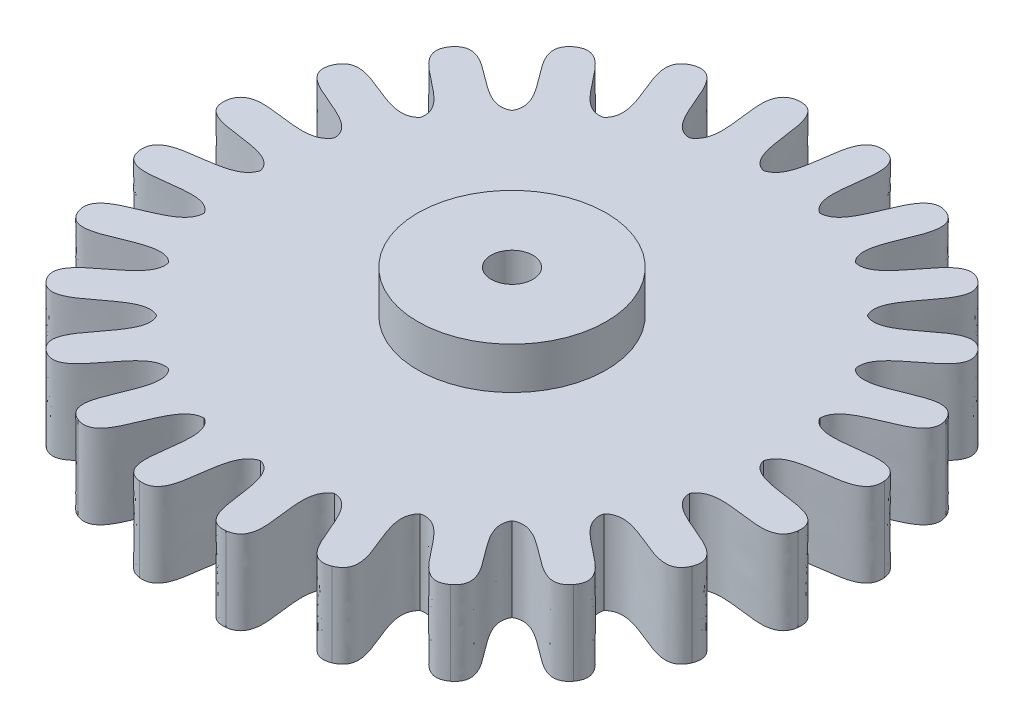
SolidWorks part; units mm, degrees
ref_plane "Front Plane" through (0, 0, 0) normal (0, 0, 1) x (1, 0, 0)
ref_plane "Top Plane" through (0, 0, 0) normal (0, 1, 0) x (1, 0, 0)
ref_plane "Right Plane" through (0, 0, 0) normal (1, 0, 0) x (0, 0, -1)
sketch "Sketch1" plane through (0, 0, 0) normal (0, 1, 0) x (1, 0, 0)
  circle A0 centre (0, 0) radius 2.25
  dimension "D1" = 4.5
extrude "Boss-Extrude1" add sketch "Sketch1" along normal blind 1
sketch "Sketch4" plane through (0, 1, 0) normal (0, 1, 0) x (1, 0, 0)
  circle A3 centre (-14, 0) radius 6
  point P4 (0, 0)
  circle B0 centre (-14, 0) radius 8
  spline B1 degree 3 poles (-14, 6) (-14.7204, 6.1976) (-14.1794, 7.9701) (-15.0353, 7.8637) knots 0 0 0 0 1 1 1 1
  spline B2 degree 3 poles (-15.5529, 5.7956) (-14.9082, 6.1729) (-15.8896, 7.745) (-15.0353, 7.8637) knots 0 0 0 0 1 1 1 1
  spline B3 degree 3 poles (-12.4471, 5.7956) (-13.0918, 6.1729) (-12.1104, 7.745) (-12.9647, 7.8637) knots 0 0 0 0 1 1 1 1
  spline B4 degree 3 poles (-14, 6) (-13.2796, 6.1976) (-13.8206, 7.9701) (-12.9647, 7.8637) knots 0 0 0 0 1 1 1 1
  spline B5 degree 3 poles (-11, 5.1962) (-11.5251, 5.7275) (-10.1703, 6.992) (-10.9647, 7.3278) knots 0 0 0 0 1 1 1 1
  spline B6 degree 3 poles (-12.4471, 5.7956) (-11.7, 5.7999) (-11.7639, 7.6521) (-10.9647, 7.3278) knots 0 0 0 0 1 1 1 1
  spline B7 degree 3 poles (-9.7574, 4.2426) (-10.1271, 4.8918) (-8.4911, 5.7626) (-9.1716, 6.2925) knots 0 0 0 0 1 1 1 1
  spline B8 degree 3 poles (-11, 5.1962) (-10.2773, 5.007) (-9.8596, 6.8127) (-9.1716, 6.2925) knots 0 0 0 0 1 1 1 1
  spline B9 degree 3 poles (-8.8038, 3) (-8.993, 3.7227) (-7.1873, 4.1404) (-7.7075, 4.8284) knots 0 0 0 0 1 1 1 1
  spline B10 degree 3 poles (-9.7574, 4.2426) (-9.1082, 3.8729) (-8.2374, 5.5089) (-7.7075, 4.8284) knots 0 0 0 0 1 1 1 1
  spline B11 degree 3 poles (-8.2044, 1.5529) (-8.2001, 2.3) (-6.3479, 2.2361) (-6.6722, 3.0353) knots 0 0 0 0 1 1 1 1
  spline B12 degree 3 poles (-8.8038, 3) (-8.2725, 2.4749) (-7.008, 3.8297) (-6.6722, 3.0353) knots 0 0 0 0 1 1 1 1
  spline B13 degree 3 poles (-8, 0) (-7.8024, 0.7204) (-6.0299, 0.1794) (-6.1363, 1.0353) knots 0 0 0 0 1 1 1 1
  spline B14 degree 3 poles (-8.2044, 1.5529) (-7.8271, 0.9082) (-6.255, 1.8896) (-6.1363, 1.0353) knots 0 0 0 0 1 1 1 1
  spline B15 degree 3 poles (-8.2044, -1.5529) (-7.8271, -0.9082) (-6.255, -1.8896) (-6.1363, -1.0353) knots 0 0 0 0 1 1 1 1
  spline B16 degree 3 poles (-8, 0) (-7.8024, -0.7204) (-6.0299, -0.1794) (-6.1363, -1.0353) knots 0 0 0 0 1 1 1 1
  spline B17 degree 3 poles (-8.8038, -3) (-8.2725, -2.4749) (-7.008, -3.8297) (-6.6722, -3.0353) knots 0 0 0 0 1 1 1 1
  spline B18 degree 3 poles (-8.2044, -1.5529) (-8.2001, -2.3) (-6.3479, -2.2361) (-6.6722, -3.0353) knots 0 0 0 0 1 1 1 1
  spline B19 degree 3 poles (-9.7574, -4.2426) (-9.1082, -3.8729) (-8.2374, -5.5089) (-7.7075, -4.8284) knots 0 0 0 0 1 1 1 1
  spline B20 degree 3 poles (-8.8038, -3) (-8.993, -3.7227) (-7.1873, -4.1404) (-7.7075, -4.8284) knots 0 0 0 0 1 1 1 1
  spline B21 degree 3 poles (-11, -5.1962) (-10.2773, -5.007) (-9.8596, -6.8127) (-9.1716, -6.2925) knots 0 0 0 0 1 1 1 1
  spline B22 degree 3 poles (-9.7574, -4.2426) (-10.1271, -4.8918) (-8.4911, -5.7626) (-9.1716, -6.2925) knots 0 0 0 0 1 1 1 1
  spline B23 degree 3 poles (-12.4471, -5.7956) (-11.7, -5.7999) (-11.7639, -7.6521) (-10.9647, -7.3278) knots 0 0 0 0 1 1 1 1
  spline B24 degree 3 poles (-11, -5.1962) (-11.5251, -5.7275) (-10.1703, -6.992) (-10.9647, -7.3278) knots 0 0 0 0 1 1 1 1
  spline B25 degree 3 poles (-14, -6) (-13.2796, -6.1976) (-13.8206, -7.9701) (-12.9647, -7.8637) knots 0 0 0 0 1 1 1 1
  spline B26 degree 3 poles (-12.4471, -5.7956) (-13.0918, -6.1729) (-12.1104, -7.745) (-12.9647, -7.8637) knots 0 0 0 0 1 1 1 1
  spline B27 degree 3 poles (-15.5529, -5.7956) (-14.9082, -6.1729) (-15.8896, -7.745) (-15.0353, -7.8637) knots 0 0 0 0 1 1 1 1
  spline B28 degree 3 poles (-14, -6) (-14.7204, -6.1976) (-14.1794, -7.9701) (-15.0353, -7.8637) knots 0 0 0 0 1 1 1 1
  spline B29 degree 3 poles (-17, -5.1962) (-16.4749, -5.7275) (-17.8297, -6.992) (-17.0353, -7.3278) knots 0 0 0 0 1 1 1 1
  spline B30 degree 3 poles (-15.5529, -5.7956) (-16.3, -5.7999) (-16.2361, -7.6521) (-17.0353, -7.3278) knots 0 0 0 0 1 1 1 1
  spline B31 degree 3 poles (-18.2426, -4.2426) (-17.8729, -4.8918) (-19.5089, -5.7626) (-18.8284, -6.2925) knots 0 0 0 0 1 1 1 1
  spline B32 degree 3 poles (-17, -5.1962) (-17.7227, -5.007) (-18.1404, -6.8127) (-18.8284, -6.2925) knots 0 0 0 0 1 1 1 1
  spline B33 degree 3 poles (-19.1962, -3) (-19.007, -3.7227) (-20.8127, -4.1404) (-20.2925, -4.8284) knots 0 0 0 0 1 1 1 1
  spline B34 degree 3 poles (-18.2426, -4.2426) (-18.8918, -3.8729) (-19.7626, -5.5089) (-20.2925, -4.8284) knots 0 0 0 0 1 1 1 1
  spline B35 degree 3 poles (-19.7956, -1.5529) (-19.7999, -2.3) (-21.6521, -2.2361) (-21.3278, -3.0353) knots 0 0 0 0 1 1 1 1
  spline B36 degree 3 poles (-19.1962, -3) (-19.7275, -2.4749) (-20.992, -3.8297) (-21.3278, -3.0353) knots 0 0 0 0 1 1 1 1
  spline B37 degree 3 poles (-20, 0) (-20.1976, -0.7204) (-21.9701, -0.1794) (-21.8637, -1.0353) knots 0 0 0 0 1 1 1 1
  spline B38 degree 3 poles (-19.7956, -1.5529) (-20.1729, -0.9082) (-21.745, -1.8896) (-21.8637, -1.0353) knots 0 0 0 0 1 1 1 1
  spline B39 degree 3 poles (-19.7956, 1.5529) (-20.1729, 0.9082) (-21.745, 1.8896) (-21.8637, 1.0353) knots 0 0 0 0 1 1 1 1
  spline B40 degree 3 poles (-20, 0) (-20.1976, 0.7204) (-21.9701, 0.1794) (-21.8637, 1.0353) knots 0 0 0 0 1 1 1 1
  spline B41 degree 3 poles (-19.1962, 3) (-19.7275, 2.4749) (-20.992, 3.8297) (-21.3278, 3.0353) knots 0 0 0 0 1 1 1 1
  spline B42 degree 3 poles (-19.7956, 1.5529) (-19.7999, 2.3) (-21.6521, 2.2361) (-21.3278, 3.0353) knots 0 0 0 0 1 1 1 1
  spline B43 degree 3 poles (-18.2426, 4.2426) (-18.8918, 3.8729) (-19.7626, 5.5089) (-20.2925, 4.8284) knots 0 0 0 0 1 1 1 1
  spline B44 degree 3 poles (-19.1962, 3) (-19.007, 3.7227) (-20.8127, 4.1404) (-20.2925, 4.8284) knots 0 0 0 0 1 1 1 1
  spline B45 degree 3 poles (-17, 5.1962) (-17.7227, 5.007) (-18.1404, 6.8127) (-18.8284, 6.2925) knots 0 0 0 0 1 1 1 1
  spline B46 degree 3 poles (-18.2426, 4.2426) (-17.8729, 4.8918) (-19.5089, 5.7626) (-18.8284, 6.2925) knots 0 0 0 0 1 1 1 1
  spline B47 degree 3 poles (-15.5529, 5.7956) (-16.3, 5.7999) (-16.2361, 7.6521) (-17.0353, 7.3278) knots 0 0 0 0 1 1 1 1
  spline B48 degree 3 poles (-17, 5.1962) (-16.4749, 5.7275) (-17.8297, 6.992) (-17.0353, 7.3278) knots 0 0 0 0 1 1 1 1
  circle B49 centre (-13.3148, 4.3262) radius 8
  spline B50 degree 3 poles (-7.323, 4.0122) (-7.088, 4.7213) (-5.3462, 4.0882) (-5.4077, 4.9485) knots 0 0 0 0 1 1 1 1
  spline B51 degree 3 poles (-7.4459, 5.5737) (-7.1029, 4.9101) (-5.4815, 5.8079) (-5.4077, 4.9485) knots 0 0 0 0 1 1 1 1
  spline B52 degree 3 poles (-7.323, 4.0122) (-7.1634, 3.2824) (-5.365, 3.73) (-5.516, 2.8808) knots 0 0 0 0 1 1 1 1
  spline B53 degree 3 poles (-8.2828, 1.0584) (-7.7247, 1.555) (-6.5328, 0.1358) (-6.1559, 0.9116) knots 0 0 0 0 1 1 1 1
  spline B54 degree 3 poles (-8.2828, 1.0584) (-8.5094, 0.3466) (-6.7282, -0.165) (-7.2836, -0.8249) knots 0 0 0 0 1 1 1 1
  spline B55 degree 3 poles (-10.5908, -1.0198) (-9.8592, -0.8688) (-9.5366, -2.6938) (-8.8223, -2.2104) knots 0 0 0 0 1 1 1 1
  spline B56 degree 3 poles (-13.6288, -1.6655) (-12.9197, -1.9006) (-13.5528, -3.6424) (-12.6925, -3.5809) knots 0 0 0 0 1 1 1 1
  spline B57 degree 3 poles (-13.6288, -1.6655) (-14.3586, -1.8251) (-13.911, -3.6236) (-14.7602, -3.4725) knots 0 0 0 0 1 1 1 1
  spline B58 degree 3 poles (-15.1689, -1.3801) (-15.9151, -1.3454) (-15.9483, -3.1984) (-16.7294, -2.8327) knots 0 0 0 0 1 1 1 1
  spline B59 degree 3 poles (-17.3296, 8.7851) (-17.9972, 8.4499) (-18.7811, 10.1292) (-19.346, 9.4774) knots 0 0 0 0 1 1 1 1
  spline B60 degree 3 poles (-13.0008, 10.318) (-13.7099, 10.553) (-13.0768, 12.2948) (-13.9371, 12.2333) knots 0 0 0 0 1 1 1 1
  circle B61 centre (-11.3262, 8.229) radius 8
  spline B62 degree 3 poles (-5.3591, 7.6018) (-5.0873, 8.2977) (-3.381, 7.5743) (-3.3974, 8.4366) knots 0 0 0 0 1 1 1 1
  spline B63 degree 3 poles (-5.4001, 9.1676) (-5.0923, 8.4869) (-3.4262, 9.2986) (-3.3974, 8.4366) knots 0 0 0 0 1 1 1 1
  spline B64 degree 3 poles (-5.7248, 6.0788) (-5.2821, 6.6806) (-3.8212, 5.5402) (-3.6138, 6.3774) knots 0 0 0 0 1 1 1 1
  spline B65 degree 3 poles (-5.3591, 7.6018) (-5.2379, 6.8647) (-3.4185, 7.2175) (-3.6138, 6.3774) knots 0 0 0 0 1 1 1 1
  spline B66 degree 3 poles (-5.7248, 6.0788) (-5.7985, 5.3354) (-3.9498, 5.2053) (-4.3558, 4.4444) knots 0 0 0 0 1 1 1 1
  spline B67 degree 3 poles (-17.2934, 8.8562) (-17.5652, 8.1603) (-19.2715, 8.8837) (-19.2551, 8.0214) knots 0 0 0 0 1 1 1 1
  spline B68 degree 3 poles (-16.1803, 11.7557) (-15.9167, 12.4547) (-17.6688, 13.0588) (-17.0796, 13.6887) knots 0 0 0 0 1 1 1 1
  circle B69 centre (-8.229, 11.3262) radius 8
  spline B70 degree 3 poles (-3.5661, 7.5503) (-2.9592, 7.9859) (-1.9222, 6.4499) (-1.4662, 7.182) knots 0 0 0 0 1 1 1 1
  spline B71 degree 3 poles (-2.7477, 8.8858) (-2.8603, 8.1473) (-1.0209, 7.9206) (-1.4662, 7.182) knots 0 0 0 0 1 1 1 1
  spline B72 degree 3 poles (-4.7023, 6.4721) (-4.0033, 6.7358) (-3.3992, 4.9837) (-2.7693, 5.5729) knots 0 0 0 0 1 1 1 1
  spline B73 degree 3 poles (-3.5661, 7.5503) (-3.866, 6.8661) (-2.1479, 6.1711) (-2.7693, 5.5729) knots 0 0 0 0 1 1 1 1
  spline B74 degree 3 poles (-4.7023, 6.4721) (-5.169, 5.8888) (-3.6894, 4.7728) (-4.4444, 4.3558) knots 0 0 0 0 1 1 1 1
  spline B75 degree 3 poles (-7.6018, 5.3591) (-6.8647, 5.2379) (-7.2175, 3.4185) (-6.3774, 3.6138) knots 0 0 0 0 1 1 1 1
  spline B76 degree 3 poles (-6.0788, 5.7248) (-6.6806, 5.2821) (-5.5402, 3.8212) (-6.3774, 3.6138) knots 0 0 0 0 1 1 1 1
  spline B77 degree 3 poles (-10.6694, 5.845) (-10.0916, 5.3714) (-11.3069, 3.9722) (-10.4817, 3.7213) knots 0 0 0 0 1 1 1 1
  spline B78 degree 3 poles (-12.0049, 6.6634) (-11.5694, 6.0564) (-13.1054, 5.0194) (-12.3732, 4.5635) knots 0 0 0 0 1 1 1 1
  spline B79 degree 3 poles (-12.0049, 6.6634) (-12.6892, 6.9632) (-13.3842, 5.2452) (-13.9823, 5.8665) knots 0 0 0 0 1 1 1 1
  spline B80 degree 3 poles (-13.0831, 7.7995) (-13.6664, 8.2662) (-14.7824, 6.7866) (-15.1994, 7.5416) knots 0 0 0 0 1 1 1 1
  spline B81 degree 3 poles (-13.7103, 13.7667) (-13.5977, 14.5052) (-15.4371, 14.7318) (-14.9918, 15.4705) knots 0 0 0 0 1 1 1 1
  circle B82 centre (-4.3262, 13.3148) radius 8
  spline B83 degree 3 poles (0.1326, 9.3) (-0.2026, 8.6324) (1.4767, 7.8484) (0.8249, 7.2836) knots 0 0 0 0 1 1 1 1
  spline B84 degree 3 poles (-2.4721, 7.6085) (-1.7259, 7.6432) (-1.6927, 5.7902) (-0.9116, 6.1559) knots 0 0 0 0 1 1 1 1
  spline B85 degree 3 poles (-1.0584, 8.2828) (-1.555, 7.7247) (-0.1358, 6.5328) (-0.9116, 6.1559) knots 0 0 0 0 1 1 1 1
  spline B86 degree 3 poles (-2.4721, 7.6085) (-3.0963, 7.1979) (-2.0339, 5.6793) (-2.8808, 5.516) knots 0 0 0 0 1 1 1 1
  spline B87 degree 3 poles (-5.5737, 7.4459) (-4.9101, 7.1029) (-5.8079, 5.4815) (-4.9485, 5.4077) knots 0 0 0 0 1 1 1 1
  spline B88 degree 3 poles (-7.0502, 7.9688) (-6.498, 7.4656) (-7.7848, 6.1319) (-6.9738, 5.8382) knots 0 0 0 0 1 1 1 1
  circle B89 centre (0, 14) radius 8
  spline B90 degree 3 poles (4.2426, 9.7574) (4.8918, 10.1271) (5.7626, 8.4911) (6.2925, 9.1716) knots 0 0 0 0 1 1 1 1
  spline B91 degree 3 poles (3, 8.8038) (3.7227, 8.993) (4.1404, 7.1873) (4.8284, 7.7075) knots 0 0 0 0 1 1 1 1
  spline B92 degree 3 poles (1.5529, 8.2044) (2.3, 8.2001) (2.2361, 6.3479) (3.0353, 6.6722) knots 0 0 0 0 1 1 1 1
  spline B93 degree 3 poles (-1.5529, 8.2044) (-0.9082, 7.8271) (-1.8896, 6.255) (-1.0353, 6.1363) knots 0 0 0 0 1 1 1 1
  spline B94 degree 3 poles (-3, 8.8038) (-2.4749, 8.2725) (-3.8297, 7.008) (-3.0353, 6.6722) knots 0 0 0 0 1 1 1 1
  spline B95 degree 3 poles (-1.5529, 8.2044) (-2.3, 8.2001) (-2.2361, 6.3479) (-3.0353, 6.6722) knots 0 0 0 0 1 1 1 1
  spline B96 degree 3 poles (-3, 8.8038) (-3.7227, 8.993) (-4.1404, 7.1873) (-4.8284, 7.7075) knots 0 0 0 0 1 1 1 1
  dimension "D1" = 14
  dimension "D2" = 0
  dimension "D3" = 6
sketch_block_instance "Block1-1"
sketch_block "Block1" parameters "D1"=16
sketch_block_instance "Block1-2"
sketch_block_instance "Block1-3"
sketch_block_instance "Block1-4"
sketch_block_instance "Block1-5"
sketch_block_instance "Block1-6"
sketch "Sketch5" plane through (0, 0, 0) normal (0, -1, 0) x (1, 0, 0)
  point P0 (0, 0)
sketch "Sketch6" plane through (0, 0, 0) normal (0, -1, 0) x (1, 0, 0)
  line B0 (0, 8) -> (0, 0) construction
  line B1 (0, 0) -> (-2.0706, 7.7274) construction
  line B2 (-2.0706, 7.7274) -> (0, 8) construction
  line B3 (-1.0353, 7.8637) -> (0, 0)
  circle B4 centre (0, 0) radius 6
  circle B5 centre (0, 0) radius 8
  circle B6 centre (0, 0) radius 2
  spline B7 degree 3 poles (0, 6) (-0.7204, 6.1976) (-0.1794, 7.9701) (-1.0353, 7.8637) knots 0 0 0 0 1 1 1 1
  spline B8 degree 3 poles (-1.5529, 5.7956) (-0.9082, 6.1729) (-1.8896, 7.745) (-1.0353, 7.8637) knots 0 0 0 0 1 1 1 1
  spline B9 degree 3 poles (1.5529, 5.7956) (0.9082, 6.1729) (1.8896, 7.745) (1.0353, 7.8637) knots 0 0 0 0 1 1 1 1
  spline B10 degree 3 poles (0, 6) (0.7204, 6.1976) (0.1794, 7.9701) (1.0353, 7.8637) knots 0 0 0 0 1 1 1 1
  spline B11 degree 3 poles (3, 5.1962) (2.4749, 5.7275) (3.8297, 6.992) (3.0353, 7.3278) knots 0 0 0 0 1 1 1 1
  spline B12 degree 3 poles (1.5529, 5.7956) (2.3, 5.7999) (2.2361, 7.6521) (3.0353, 7.3278) knots 0 0 0 0 1 1 1 1
  spline B13 degree 3 poles (4.2426, 4.2426) (3.8729, 4.8918) (5.5089, 5.7626) (4.8284, 6.2925) knots 0 0 0 0 1 1 1 1
  spline B14 degree 3 poles (3, 5.1962) (3.7227, 5.007) (4.1404, 6.8127) (4.8284, 6.2925) knots 0 0 0 0 1 1 1 1
  spline B15 degree 3 poles (5.1962, 3) (5.007, 3.7227) (6.8127, 4.1404) (6.2925, 4.8284) knots 0 0 0 0 1 1 1 1
  spline B16 degree 3 poles (4.2426, 4.2426) (4.8918, 3.8729) (5.7626, 5.5089) (6.2925, 4.8284) knots 0 0 0 0 1 1 1 1
  spline B17 degree 3 poles (5.7956, 1.5529) (5.7999, 2.3) (7.6521, 2.2361) (7.3278, 3.0353) knots 0 0 0 0 1 1 1 1
  spline B18 degree 3 poles (5.1962, 3) (5.7275, 2.4749) (6.992, 3.8297) (7.3278, 3.0353) knots 0 0 0 0 1 1 1 1
  spline B19 degree 3 poles (6, 0) (6.1976, 0.7204) (7.9701, 0.1794) (7.8637, 1.0353) knots 0 0 0 0 1 1 1 1
  spline B20 degree 3 poles (5.7956, 1.5529) (6.1729, 0.9082) (7.745, 1.8896) (7.8637, 1.0353) knots 0 0 0 0 1 1 1 1
  spline B21 degree 3 poles (5.7956, -1.5529) (6.1729, -0.9082) (7.745, -1.8896) (7.8637, -1.0353) knots 0 0 0 0 1 1 1 1
  spline B22 degree 3 poles (6, 0) (6.1976, -0.7204) (7.9701, -0.1794) (7.8637, -1.0353) knots 0 0 0 0 1 1 1 1
  spline B23 degree 3 poles (5.1962, -3) (5.7275, -2.4749) (6.992, -3.8297) (7.3278, -3.0353) knots 0 0 0 0 1 1 1 1
  spline B24 degree 3 poles (5.7956, -1.5529) (5.7999, -2.3) (7.6521, -2.2361) (7.3278, -3.0353) knots 0 0 0 0 1 1 1 1
  spline B25 degree 3 poles (4.2426, -4.2426) (4.8918, -3.8729) (5.7626, -5.5089) (6.2925, -4.8284) knots 0 0 0 0 1 1 1 1
  spline B26 degree 3 poles (5.1962, -3) (5.007, -3.7227) (6.8127, -4.1404) (6.2925, -4.8284) knots 0 0 0 0 1 1 1 1
  spline B27 degree 3 poles (3, -5.1962) (3.7227, -5.007) (4.1404, -6.8127) (4.8284, -6.2925) knots 0 0 0 0 1 1 1 1
  spline B28 degree 3 poles (4.2426, -4.2426) (3.8729, -4.8918) (5.5089, -5.7626) (4.8284, -6.2925) knots 0 0 0 0 1 1 1 1
  spline B29 degree 3 poles (1.5529, -5.7956) (2.3, -5.7999) (2.2361, -7.6521) (3.0353, -7.3278) knots 0 0 0 0 1 1 1 1
  spline B30 degree 3 poles (3, -5.1962) (2.4749, -5.7275) (3.8297, -6.992) (3.0353, -7.3278) knots 0 0 0 0 1 1 1 1
  spline B31 degree 3 poles (0, -6) (0.7204, -6.1976) (0.1794, -7.9701) (1.0353, -7.8637) knots 0 0 0 0 1 1 1 1
  spline B32 degree 3 poles (1.5529, -5.7956) (0.9082, -6.1729) (1.8896, -7.745) (1.0353, -7.8637) knots 0 0 0 0 1 1 1 1
  spline B33 degree 3 poles (-1.5529, -5.7956) (-0.9082, -6.1729) (-1.8896, -7.745) (-1.0353, -7.8637) knots 0 0 0 0 1 1 1 1
  spline B34 degree 3 poles (0, -6) (-0.7204, -6.1976) (-0.1794, -7.9701) (-1.0353, -7.8637) knots 0 0 0 0 1 1 1 1
  spline B35 degree 3 poles (-3, -5.1962) (-2.4749, -5.7275) (-3.8297, -6.992) (-3.0353, -7.3278) knots 0 0 0 0 1 1 1 1
  spline B36 degree 3 poles (-1.5529, -5.7956) (-2.3, -5.7999) (-2.2361, -7.6521) (-3.0353, -7.3278) knots 0 0 0 0 1 1 1 1
  spline B37 degree 3 poles (-4.2426, -4.2426) (-3.8729, -4.8918) (-5.5089, -5.7626) (-4.8284, -6.2925) knots 0 0 0 0 1 1 1 1
  spline B38 degree 3 poles (-3, -5.1962) (-3.7227, -5.007) (-4.1404, -6.8127) (-4.8284, -6.2925) knots 0 0 0 0 1 1 1 1
  spline B39 degree 3 poles (-5.1962, -3) (-5.007, -3.7227) (-6.8127, -4.1404) (-6.2925, -4.8284) knots 0 0 0 0 1 1 1 1
  spline B40 degree 3 poles (-4.2426, -4.2426) (-4.8918, -3.8729) (-5.7626, -5.5089) (-6.2925, -4.8284) knots 0 0 0 0 1 1 1 1
  spline B41 degree 3 poles (-5.7956, -1.5529) (-5.7999, -2.3) (-7.6521, -2.2361) (-7.3278, -3.0353) knots 0 0 0 0 1 1 1 1
  spline B42 degree 3 poles (-5.1962, -3) (-5.7275, -2.4749) (-6.992, -3.8297) (-7.3278, -3.0353) knots 0 0 0 0 1 1 1 1
  spline B43 degree 3 poles (-6, 0) (-6.1976, -0.7204) (-7.9701, -0.1794) (-7.8637, -1.0353) knots 0 0 0 0 1 1 1 1
  spline B44 degree 3 poles (-5.7956, -1.5529) (-6.1729, -0.9082) (-7.745, -1.8896) (-7.8637, -1.0353) knots 0 0 0 0 1 1 1 1
  spline B45 degree 3 poles (-5.7956, 1.5529) (-6.1729, 0.9082) (-7.745, 1.8896) (-7.8637, 1.0353) knots 0 0 0 0 1 1 1 1
  spline B46 degree 3 poles (-6, 0) (-6.1976, 0.7204) (-7.9701, 0.1794) (-7.8637, 1.0353) knots 0 0 0 0 1 1 1 1
  spline B47 degree 3 poles (-5.1962, 3) (-5.7275, 2.4749) (-6.992, 3.8297) (-7.3278, 3.0353) knots 0 0 0 0 1 1 1 1
  spline B48 degree 3 poles (-5.7956, 1.5529) (-5.7999, 2.3) (-7.6521, 2.2361) (-7.3278, 3.0353) knots 0 0 0 0 1 1 1 1
  spline B49 degree 3 poles (-4.2426, 4.2426) (-4.8918, 3.8729) (-5.7626, 5.5089) (-6.2925, 4.8284) knots 0 0 0 0 1 1 1 1
  spline B50 degree 3 poles (-5.1962, 3) (-5.007, 3.7227) (-6.8127, 4.1404) (-6.2925, 4.8284) knots 0 0 0 0 1 1 1 1
  spline B51 degree 3 poles (-3, 5.1962) (-3.7227, 5.007) (-4.1404, 6.8127) (-4.8284, 6.2925) knots 0 0 0 0 1 1 1 1
  spline B52 degree 3 poles (-4.2426, 4.2426) (-3.8729, 4.8918) (-5.5089, 5.7626) (-4.8284, 6.2925) knots 0 0 0 0 1 1 1 1
  spline B53 degree 3 poles (-1.5529, 5.7956) (-2.3, 5.7999) (-2.2361, 7.6521) (-3.0353, 7.3278) knots 0 0 0 0 1 1 1 1
  spline B54 degree 3 poles (-3, 5.1962) (-2.4749, 5.7275) (-3.8297, 6.992) (-3.0353, 7.3278) knots 0 0 0 0 1 1 1 1
sketch_block_instance "Block2-1"
sketch_block "Block2"
extrude "Boss-Extrude3" add sketch "Sketch6" along normal blind 2
sketch "Sketch7" plane through (0, 1, 0) normal (0, 1, 0) x (1, 0, 0)
  circle A0 centre (0, 0) radius 0.5
  dimension "D1" = 1
extrude "Cut-Extrude1" cut sketch "Sketch7" against normal blind 10
